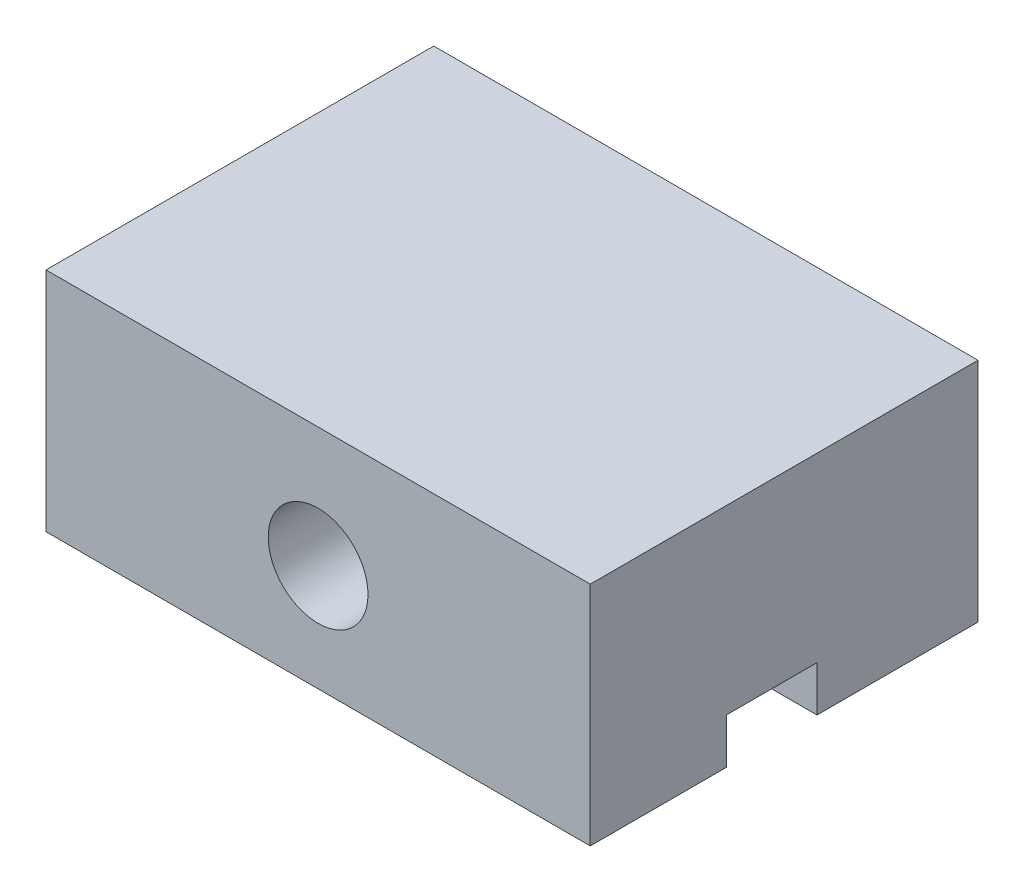
SolidWorks part; units mm, degrees
ref_plane "Płaszczyzna przednia" through (0, 0, 0) normal (0, 0, 1) x (1, 0, 0)
ref_plane "Płaszczyzna górna" through (0, 0, 0) normal (0, 1, 0) x (1, 0, 0)
ref_plane "Płaszczyzna prawa" through (0, 0, 0) normal (1, 0, 0) x (0, 0, -1)
sketch "Szkic1" plane through (0, 0, 0) normal (0, 0, 1) x (1, 0, 0)
  line L1 (-6, -2.5) -> (6, -2.5)
  line L2 (-6, -2.5) -> (-6, 2.5)
  line L3 (-6, 2.5) -> (6, 2.5)
  line L4 (6, -2.5) -> (6, 2.5)
  line L5 (-6, -2.5) -> (6, 2.5) construction
  line L6 (-6, 2.5) -> (6, -2.5) construction
  point P0 (0, 0)
  dimension "D1" = 12
  dimension "D2" = 5
extrude "Dodanie-wyciągnięcie1" add sketch "Szkic1" along normal blind 8.55
sketch "Szkic2" plane through (0, 0, 8.55) normal (0, 0, 1) x (1, 0, 0)
  line L1 (6, 2.5) -> (-6, 2.5) construction
  circle A1 centre (0, -0.15) radius 1.1
  dimension "D1" = 2.2
  dimension "D2" = 2.65
extrude "Wytnij-wyciągnięcie1" cut sketch "Szkic2" against normal through all
sketch "Szkic3" plane through (0, -2.5, 0) normal (0, -1, 0) x (-1, 0, 0)
  line L0 (6, -8.55) -> (6, 0) construction
  line L1 (6, -3.55) -> (-6, -3.55)
  line L2 (6, -3.55) -> (6, -5.55)
  line L3 (6, -5.55) -> (-6, -5.55)
  line L4 (-6, -3.55) -> (-6, -5.55)
  line L5 (6, -3.55) -> (-6, -5.55) construction
  line L6 (6, -5.55) -> (-6, -3.55) construction
  line L7 (-6, -8.55) -> (-6, 0) construction
  line L8 (6, -8.55) -> (-6, -8.55) construction
  point P0 (0, -4.55)
  dimension "D1" = 0
  dimension "D2" = 0
  dimension "D3" = 2
  dimension "D4" = 3
extrude "Wytnij-wyciągnięcie2" cut sketch "Szkic3" against normal blind 1
